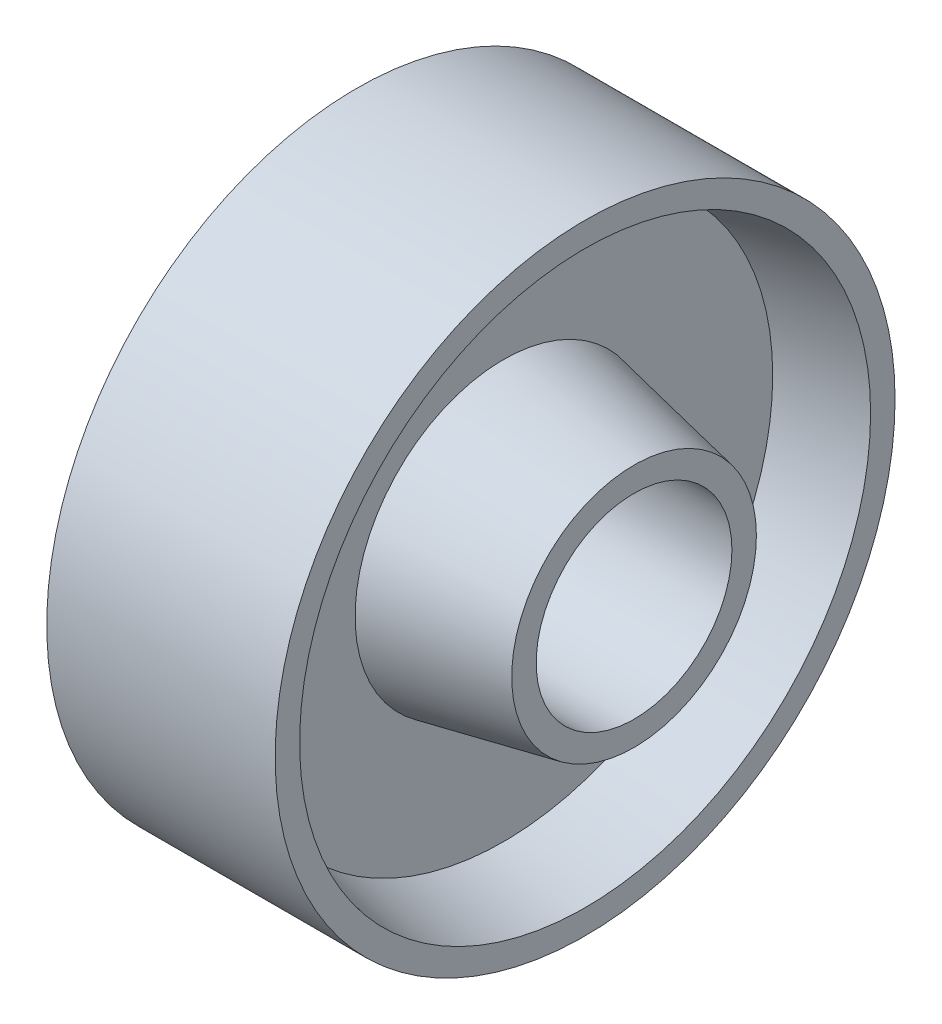
SolidWorks part; units mm, degrees
ref_plane "Front Plane" through (0, 0, 0) normal (0, 0, 1) x (1, 0, 0)
ref_plane "Top Plane" through (0, 0, 0) normal (0, 1, 0) x (1, 0, 0)
ref_plane "Right Plane" through (0, 0, 0) normal (1, 0, 0) x (0, 0, -1)
sketch "Sketch2" plane through (0, 0, 0) normal (0, 0, 1) x (1, 0, 0)
  line L0 (26.1021, 0) -> (0, 0) construction
  line L1 (0, 0) -> (0, 55.8417) construction
  line L2 (20, 15) -> (20, 12)
  line L3 (-20, 15) -> (-20, 12)
  line L4 (4, 18.2) -> (20, 15)
  line L5 (-4, 18.2) -> (-20, 15)
  line L6 (4, 18.2) -> (4, 33)
  line L7 (-4, 18.2) -> (-4, 33)
  line L8 (4, 33) -> (14, 35)
  line L9 (-4, 33) -> (-14, 35)
  line L10 (14, 35) -> (14, 38)
  line L11 (-14, 35) -> (-14, 38)
  line L12 (-14, 38) -> (14, 38)
  line L13 (-20, 12) -> (20, 12)
  dimension "D1" = 24
  dimension "D2" = 30
  dimension "D3" = 40
  dimension "D4" = 66
  dimension "D5" = 70
  dimension "D6" = 76
  dimension "D7" = 28
  dimension "D8" = 8
revolve "Revolve1" add sketch "Sketch2" angle 360 about L0
